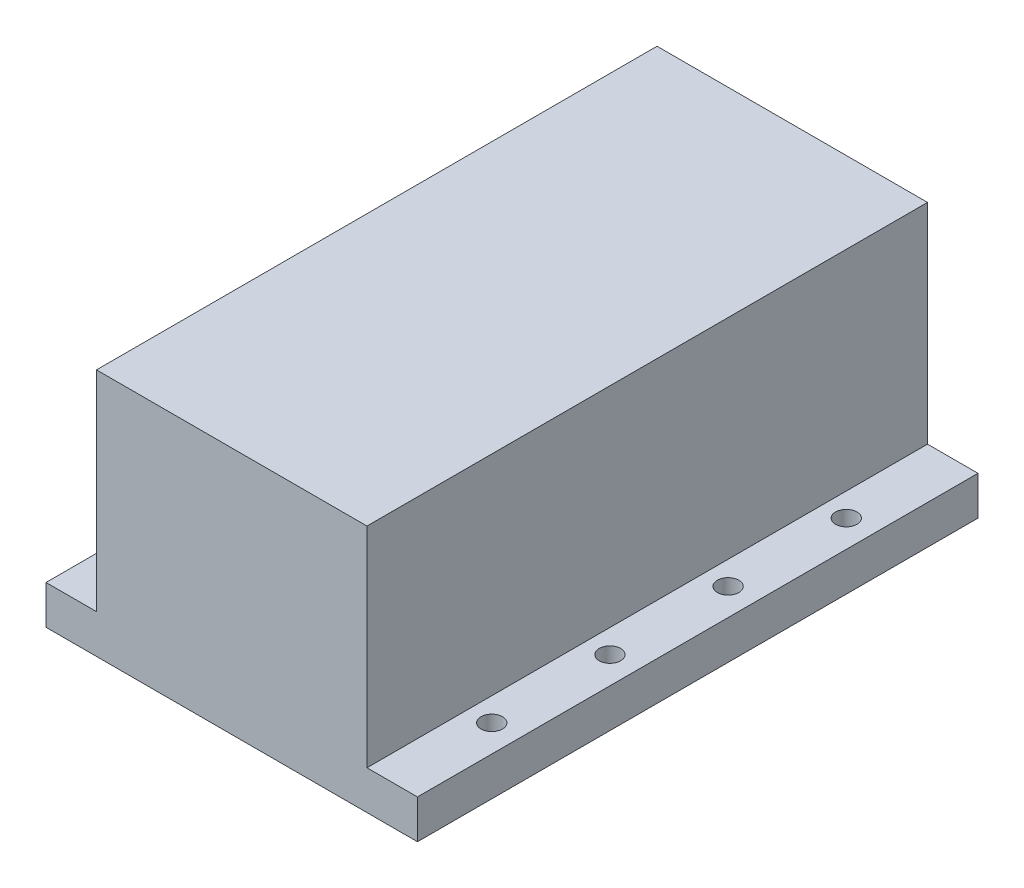
SolidWorks part; units mm, degrees
ref_plane "Front Plane" through (0, 0, 0) normal (0, 0, 1) x (1, 0, 0)
ref_plane "Top Plane" through (0, 0, 0) normal (0, 1, 0) x (1, 0, 0)
ref_plane "Right Plane" through (0, 0, 0) normal (1, 0, 0) x (0, 0, -1)
sketch "Sketch1" plane through (0, 0, 0) normal (0, 1, 0) x (1, 0, 0)
  line L1 (0, 0) -> (110, 0)
  line L2 (0, 0) -> (0, 166)
  line L3 (0, 166) -> (110, 166)
  line L4 (110, 0) -> (110, 166)
  line L5 (0, 0) -> (110, 166) construction
  line L6 (0, 166) -> (110, 0) construction
  circle A0 centre (8, 135) radius 3.175
  circle A1 centre (102, 135) radius 3.175
  circle A2 centre (102, 100) radius 3.175
  circle A3 centre (102, 65) radius 3.175
  circle A4 centre (102, 30) radius 3.175
  circle A5 centre (8, 100) radius 3.175
  circle A6 centre (8, 65) radius 3.175
  circle A7 centre (8, 30) radius 3.175
  point P4 (55, 83)
  point P8 (17.3815, 152.9274)
  point P9 (14.7592, 133.0421)
  point P10 (0, 0)
  dimension "D8" = 6.35
  dimension "D1" = 110
  dimension "D2" = 166
  dimension "D5" = 35
  dimension "D6" = 30
  dimension "D7" = 8
  dimension "D9" = 8
  dimension "D3" = 2
  dimension "D4" = 4
extrude "Boss-Extrude1" add sketch "Sketch1" along normal blind 11.5
sketch "Sketch2" plane through (0, 11.5, 0) normal (0, 1, 0) x (1, 0, 0)
  line L0 (110, 166) -> (0, 166) construction
  line L1 (14.95, 166) -> (95.05, 166)
  line L2 (14.95, 166) -> (14.95, 0)
  line L3 (14.95, 0) -> (95.05, 0)
  line L4 (95.05, 166) -> (95.05, 0)
  line L5 (14.95, 166) -> (95.05, 0) construction
  line L6 (14.95, 0) -> (95.05, 166) construction
  line L7 (0, 0) -> (110, 0) construction
  line L8 (55, 0) -> (55, 83) construction
  point P4 (55, 83)
  dimension "D1" = 80.1
extrude "Boss-Extrude2" add sketch "Sketch2" along normal blind 62
